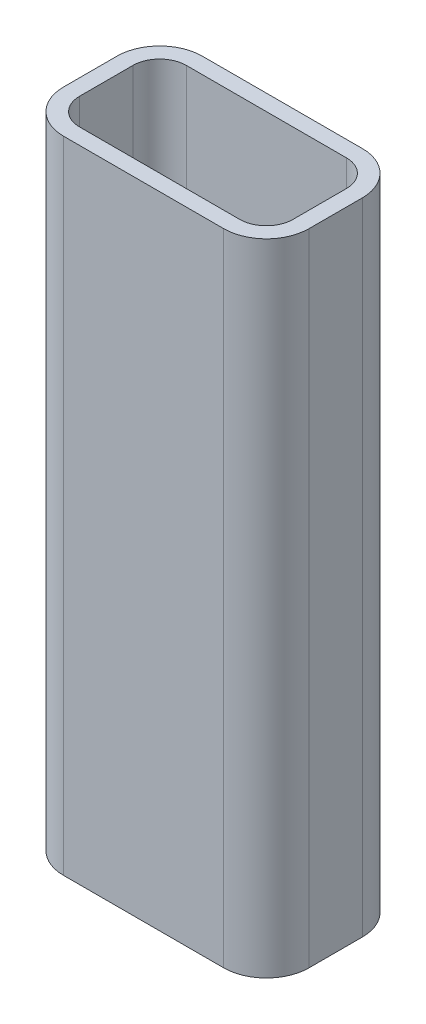
SolidWorks part; units mm, degrees
ref_plane "Front Plane" through (0, 0, 0) normal (0, 0, 1) x (1, 0, 0)
ref_plane "Top Plane" through (0, 0, 0) normal (0, 1, 0) x (1, 0, 0)
ref_plane "Right Plane" through (0, 0, 0) normal (1, 0, 0) x (0, 0, -1)
sketch "Sketch1" plane through (0, 0, 0) normal (0, 1, 0) x (1, 0, 0)
  line L1 (15, -10) -> (-15, -10)
  line L2 (20, -5) -> (20, 5)
  line L3 (15, 10) -> (-15, 10)
  line L4 (-20, -5) -> (-20, 5)
  line L5 (20, -10) -> (-20, 10) construction
  line L6 (20, 10) -> (-20, -10) construction
  arc A0 (-15, 10) -> (-20, 5) centre (-15, 5) ccw
  arc A1 (-15, -10) -> (-20, -5) centre (-15, -5) cw
  arc A2 (15, -10) -> (20, -5) centre (15, -5) ccw
  arc A3 (20, 5) -> (15, 10) centre (15, 5) ccw
  point P0 (0, 0)
  dimension "D3" = 5
  dimension "width" = 20
  dimension "height" = 40
extrude "Extrude-Thin1" add sketch "Sketch1" along normal blind 120 thin thin type one direction wall 3
sketch "Sketch2" plane through (0, 0, 0) normal (0, 0, 1) x (1, 0, 0)
  line L0 (0, 105) -> (0, 15) construction
  line L1 (6, 105) -> (6, 15)
  line L2 (-6, 105) -> (-6, 15)
  line L3 (-23, 60) -> (23, 60) construction
  line L4 (-23, 120) -> (-23, 0) construction
  line L5 (23, 120) -> (23, 0) construction
  line L6 (0, 132.8068) -> (0, -5.1109) construction
  arc A0 (6, 105) -> (-6, 105) centre (0, 105) ccw
  arc A1 (-6, 15) -> (6, 15) centre (0, 15) ccw
  point P3 (0, 60)
  dimension "D2" = 6
  dimension "D1" = 90
extrude "Cut-Extrude1" [suppressed] cut sketch "Sketch2" against normal through all both and the other way through all
